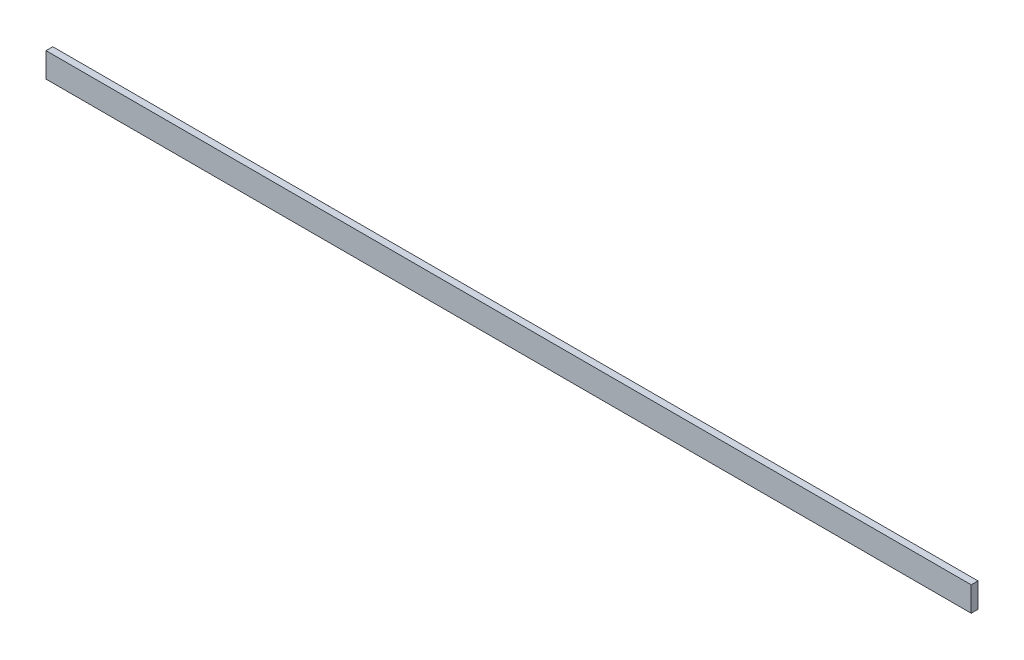
SolidWorks part; units mm, degrees
ref_plane "Face" through (0, 0, 0) normal (0, 0, 1) x (1, 0, 0)
ref_plane "Dessus" through (0, 0, 0) normal (0, 1, 0) x (1, 0, 0)
ref_plane "Droite" through (0, 0, 0) normal (1, 0, 0) x (0, 0, -1)
sketch "Esquisse1" plane through (0, 0, 0) normal (0, 1, 0) x (1, 0, 0)
  line L1 (0, 0) -> (3000, 0)
  line L2 (0, 0) -> (0, 22)
  line L3 (0, 22) -> (3000, 22)
  line L4 (3000, 0) -> (3000, 22)
  dimension "D1" = 3000
  dimension "D2" = 22
extrude "Extrusion1" add sketch "Esquisse1" along normal blind 80
